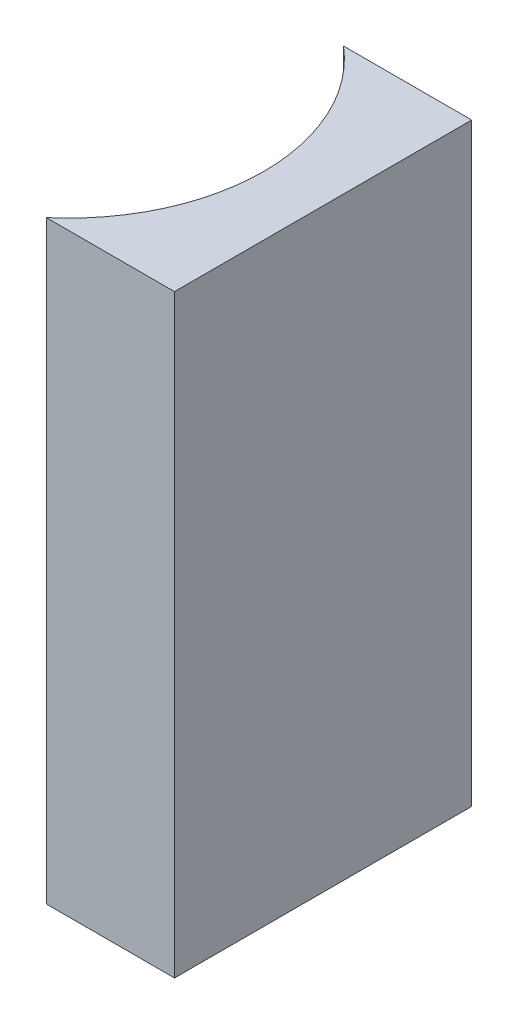
SolidWorks part; units mm, degrees
ref_plane "前视基准面" through (0, 0, 0) normal (0, 0, 1) x (1, 0, 0)
ref_plane "上视基准面" through (0, 0, 0) normal (0, 1, 0) x (1, 0, 0)
ref_plane "右视基准面" through (0, 0, 0) normal (1, 0, 0) x (0, 0, -1)
sketch "草图1" plane through (0, 0, 0) normal (0, 1, 0) x (1, 0, 0)
  line L0 (0, 0) -> (0, -10)
  line L1 (0, 0) -> (-4.3134, 0)
  line L2 (0, -10) -> (-4.3134, -10)
  line L3 (8.2336, -5) -> (-10.4405, -5) construction
  arc A0 (-4.3134, -10) -> (-4.3134, 0) centre (-8.56, -5) ccw
  point P7 (-2, -5)
  point P8 (0, -5)
  dimension "D2" = 6.56
  dimension "D3" = 2
  dimension "D1" = 10
extrude "凸台-拉伸1" add sketch "草图1" along normal blind 20
